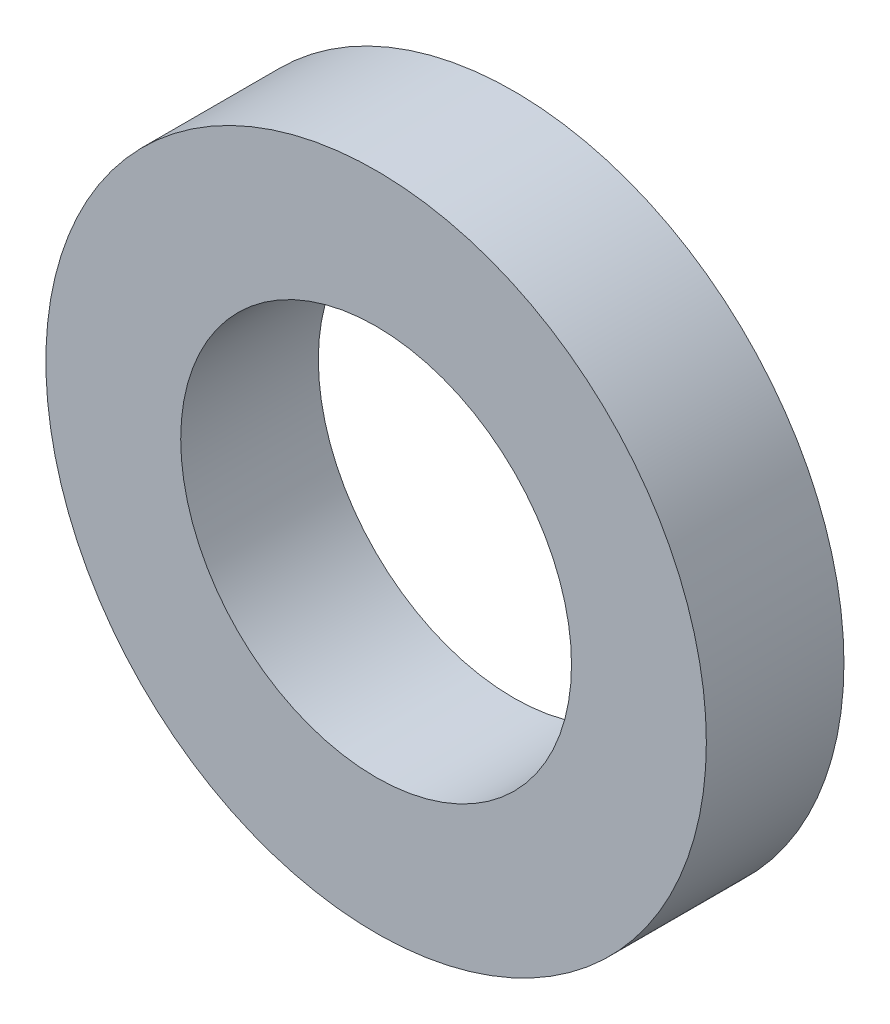
SolidWorks part; units mm, degrees
ref_plane "Front Plane" through (0, 0, 0) normal (0, 0, 1) x (1, 0, 0)
ref_plane "Top Plane" through (0, 0, 0) normal (0, 1, 0) x (1, 0, 0)
ref_plane "Right Plane" through (0, 0, 0) normal (1, 0, 0) x (0, 0, -1)
sketch "Sketch1" plane through (0, 0, 0) normal (0, 0, 1) x (1, 0, 0)
  circle A0 centre (0, 0) radius 3.55
  circle A1 centre (0, 0) radius 6
extrude "Boss-Extrude1" add sketch "Sketch1" along normal blind 2.5
